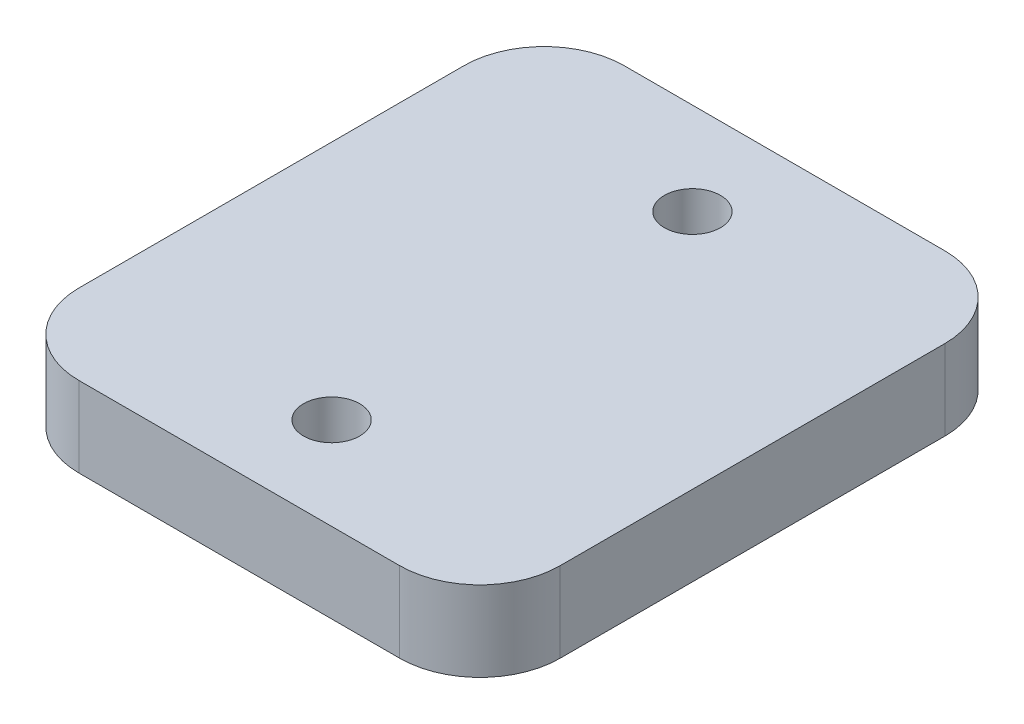
SolidWorks part; units mm, degrees
material "PLA"
ref_plane "Front Plane" through (0, 0, 0) normal (0, 0, 1) x (1, 0, 0)
ref_plane "Top Plane" through (0, 0, 0) normal (0, 1, 0) x (1, 0, 0)
ref_plane "Right Plane" through (0, 0, 0) normal (1, 0, 0) x (0, 0, -1)
ref_plane "Plane1" through (0, -5, 0) normal (0, -1, 0) x (1, 0, 0)
sketch "Sketch1" plane through (0, -5, 0) normal (0, -1, 0) x (1, 0, 0)
  line L0 (-15, 17) -> (-15, -17)
  line L1 (-15, -17) -> (15, -17)
  line L2 (15, -17) -> (15, 17)
  line L3 (15, 17) -> (-15, 17)
  line L4 (-15, 17) -> (15, -17) construction
  dimension "D1" = 30
  dimension "D2" = 34
extrude "Boss-Extrude1" add sketch "Sketch1" against normal blind 5
fillet "Fillet2" radius 5 4 edges at (-15, -2.5, -17) (-15, -2.5, 17) (15, -2.5, -17) (15, -2.5, 17)
sketch "Sketch10" plane through (0, -5, 0) normal (0, -1, 0) x (1, 0, 0)
  line L0 (10, 17) -> (-10, 17) construction
  line L2 (-15, 12) -> (-15, -12) construction
  line L3 (-15, 0) -> (15, 0) construction
  line L4 (15, -12) -> (15, 12) construction
  line L5 (0, 17) -> (0, -17) construction
  line L6 (-10, -17) -> (10, -17) construction
  circle A4 centre (0, 11.25) radius 1.75
  circle A5 centre (0, -11.25) radius 1.75
  dimension "D1" = 3.5
  dimension "D4" = 5.75
extrude "Cut-Extrude7" cut sketch "Sketch10" against normal through all
sketch "Sketch11" plane through (0, -5, 0) normal (0, -1, 0) x (1, 0, 0)
  line L0 (-15, 0) -> (15, 0) construction
  line L1 (-14.3668, 5.5) -> (-10.6332, 5.5)
  line L2 (-14.3668, 5.5) -> (-14.3668, -5.5)
  line L3 (-14.3668, -5.5) -> (-10.6332, -5.5)
  line L4 (-10.6332, 5.5) -> (-10.6332, -5.5)
  line L5 (-15, 12) -> (-15, -12) construction
  line L6 (15, -12) -> (15, 12) construction
  line L7 (-9.3668, 5.5) -> (-5.6332, 5.5)
  line L8 (-9.3668, 5.5) -> (-9.3668, -5.5)
  line L9 (-5.6332, 5.5) -> (-5.6332, -5.5)
  line L10 (-9.3668, -5.5) -> (-5.6332, -5.5)
  line L11 (-4.3668, 5.5) -> (-0.6332, 5.5)
  line L12 (-4.3668, 5.5) -> (-4.3668, -5.5)
  line L13 (-0.6332, 5.5) -> (-0.6332, -5.5)
  line L14 (-4.3668, -5.5) -> (-0.6332, -5.5)
  line L15 (0.6332, 5.5) -> (4.3668, 5.5)
  line L16 (0.6332, 5.5) -> (0.6332, -5.5)
  line L17 (4.3668, 5.5) -> (4.3668, -5.5)
  line L18 (0.6332, -5.5) -> (4.3668, -5.5)
  line L19 (5.6332, 5.5) -> (9.3668, 5.5)
  line L20 (5.6332, 5.5) -> (5.6332, -5.5)
  line L21 (9.3668, 5.5) -> (9.3668, -5.5)
  line L22 (5.6332, -5.5) -> (9.3668, -5.5)
  line L23 (10.6332, 5.5) -> (14.3668, 5.5)
  line L24 (10.6332, 5.5) -> (10.6332, -5.5)
  line L25 (14.3668, 5.5) -> (14.3668, -5.5)
  line L26 (10.6332, -5.5) -> (14.3668, -5.5)
  point P14 (-10.6332, 0)
  dimension "D1" = 11
  dimension "D2" = 3.7337
  dimension "D3" = 0.6332
  dimension "D4" = 6
extrude "Cut-Extrude8" cut sketch "Sketch11" against normal blind 1.2
draft "Draft1" type of draft neutral plane draft angle 20 faces to draft 12 face at (10.6332, -4.4, 0) face at (5.6332, -4.4, 0) face at (0.6332, -4.4, 0) face at (-4.3668, -4.4, 0) face at (-9.3668, -4.4, 0) face at (-14.3668, -4.4, 0) face at (14.3668, -4.4, 0) face at (9.3668, -4.4, 0) face at (4.3668, -4.4, 0) face at (-0.6332, -4.4, 0) face at (-5.6332, -4.4, 0) face at (-10.6332, -4.4, 0) neutral plane through (0, -5, 0) neutral plane normal (0, -1, 0) parameters "D1"=20
fillet "Fillet3" radius 0.4 24 edges at (-10.6332, -5, 0) (-11.0699, -3.8, 0) (-5.6332, -5, 0) (-6.0699, -3.8, 0) (-0.6332, -5, 0) (-1.0699, -3.8, 0) (4.3668, -5, 0) (3.9301, -3.8, 0) (9.3668, -5, 0) (8.9301, -3.8, 0) (14.3668, -5, 0) (13.9301, -3.8, 0) (10.6332, -5, 0) (11.0699, -3.8, 0) (5.6332, -5, 0) (6.0699, -3.8, 0) (0.6332, -5, 0) (1.0699, -3.8, 0) (-3.9301, -3.8, 0) (-4.3668, -5, 0) (-9.3668, -5, 0) (-8.9301, -3.8, 0) (-14.3668, -5, 0) (-13.9301, -3.8, 0)
